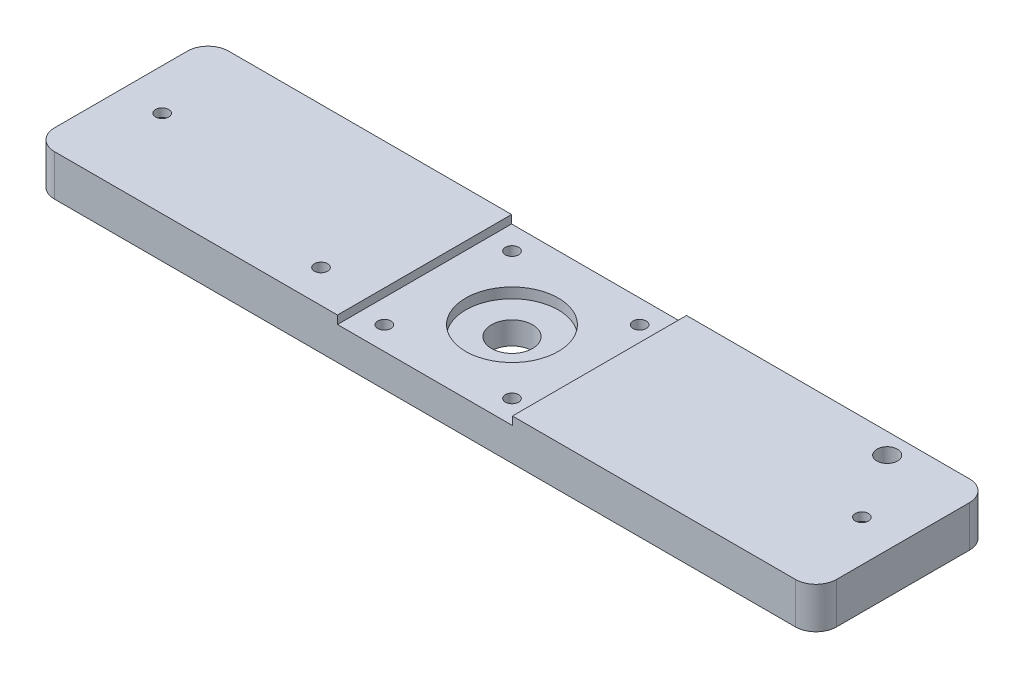
SolidWorks part; units mm, degrees
ref_plane "前视基准面" through (0, 0, 0) normal (0, 0, 1) x (1, 0, 0)
ref_plane "上视基准面" through (0, 0, 0) normal (0, 1, 0) x (1, 0, 0)
ref_plane "右视基准面" through (0, 0, 0) normal (1, 0, 0) x (0, 0, -1)
sketch "草图1" plane through (0, 0, 0) normal (0, 1, 0) x (1, 0, 0)
  line L1 (-95, 21.15) -> (95, 21.15)
  line L2 (-95, 21.15) -> (-95, -21.15)
  line L3 (-95, -21.15) -> (95, -21.15)
  line L4 (95, 21.15) -> (95, -21.15)
  line L5 (-95, 21.15) -> (95, -21.15) construction
  line L6 (-95, -21.15) -> (95, 21.15) construction
  point P0 (0, 0)
  dimension "D1" = 190
  dimension "D2" = 42.3
extrude "凸台-拉伸1" add sketch "草图1" along normal blind 10
sketch "草图2" plane through (0, 10, 0) normal (0, 1, 0) x (1, 0, 0)
  line L1 (-21.25, 24.8386) -> (21.25, 24.8386)
  line L2 (-21.25, 24.8386) -> (-21.25, -24.8386)
  line L3 (-21.25, -24.8386) -> (21.25, -24.8386)
  line L4 (21.25, 24.8386) -> (21.25, -24.8386)
  line L5 (-21.25, 24.8386) -> (21.25, -24.8386) construction
  line L6 (-21.25, -24.8386) -> (21.25, 24.8386) construction
  point P0 (0, 0)
  dimension "D1" = 42.5
extrude "切除-拉伸1" cut sketch "草图2" against normal blind 2
sketch "草图3" plane through (0, 8, 0) normal (0, 1, 0) x (1, 0, 0)
  line L0 (0, 0) -> (0, 29.0603) construction
  line L1 (0, 0) -> (-46.2651, 0) construction
  circle A0 centre (-15.5, 15.5) radius 1.6
  circle A1 centre (15.5, 15.5) radius 1.6
  circle A2 centre (15.5, -15.5) radius 1.6
  circle A3 centre (-15.5, -15.5) radius 1.6
  circle A4 centre (0, 0) radius 11.25
  dimension "D1" = 3.2
  dimension "D4" = 22.5
  dimension "D2" = 31
  dimension "D3" = 31
extrude "切除-拉伸2" cut sketch "草图3" against normal blind 2.5
sketch "草图4" plane through (0, 5.5, 0) normal (0, 1, 0) x (1, 0, 0)
  circle A0 centre (0, 0) radius 5
  dimension "D1" = 10
extrude "切除-拉伸3" cut sketch "草图4" against normal through all
sketch "草图5" plane through (0, 0, 0) normal (0, -1, 0) x (1, 0, 0)
  line L0 (0, 0) -> (0, 26.747) construction
  circle A0 centre (-85, 0) radius 4.025
  circle A1 centre (85, 0) radius 4.025
  dimension "D1" = 8.05
  dimension "D2" = 170
extrude "切除-拉伸4" cut sketch "草图5" against normal blind 8
sketch "草图6" plane through (0, 8, 0) normal (0, -1, 0) x (1, 0, 0)
  circle A0 centre (-85, 0) radius 1.6
  dimension "D1" = 3.2
extrude "切除-拉伸5" cut sketch "草图6" against normal through all
sketch "草图7" plane through (0, 8, 0) normal (0, -1, 0) x (1, 0, 0)
  circle A0 centre (85, 0) radius 1.6
  dimension "D1" = 3.2
extrude "切除-拉伸6" cut sketch "草图7" against normal through all
fillet "圆角1" radius 5 4 edges at (95, 5, -21.15) (95, 5, 21.15) (-95, 5, 21.15) (-95, 5, -21.15)
sketch "草图8" plane through (0, 8, 0) normal (0, 1, 0) x (1, 0, 0)
  circle A0 centre (15.5, 15.5) radius 1.6 construction
  circle A1 centre (15.5, -15.5) radius 1.6 construction
  circle A2 centre (-15.5, -15.5) radius 1.6 construction
  circle A3 centre (-15.5, 15.5) radius 1.6 construction
  circle A4 centre (15.5, 15.5) radius 1.6
  circle A5 centre (15.5, -15.5) radius 1.6
  circle A6 centre (-15.5, -15.5) radius 1.6
  circle A7 centre (-15.5, 15.5) radius 1.6
extrude "切除-拉伸7" cut sketch "草图8" against normal through all
sketch "草图9" plane through (0, 10, 0) normal (0, 1, 0) x (1, 0, 0)
  line L0 (-21.25, 21.15) -> (-21.25, -21.15) construction
  line L1 (-90, -21.15) -> (-21.25, -21.15) construction
  circle A0 centre (-33.25, -13.15) radius 1.6
  dimension "D1" = 3.2
  dimension "D2" = 12
  dimension "D3" = 8
extrude "切除-拉伸8" cut sketch "草图9" against normal up to next
sketch "草图11" plane through (0, 10, 0) normal (0, 1, 0) x (1, 0, 0)
  line L0 (90, 21.15) -> (21.25, 21.15) construction
  line L1 (95, -16.15) -> (95, 16.15) construction
  circle A0 centre (75, 16.15) radius 2.5
  dimension "D1" = 5
  dimension "D2" = 5
  dimension "D3" = 20
extrude "切除-拉伸9" cut sketch "草图11" against normal through all
